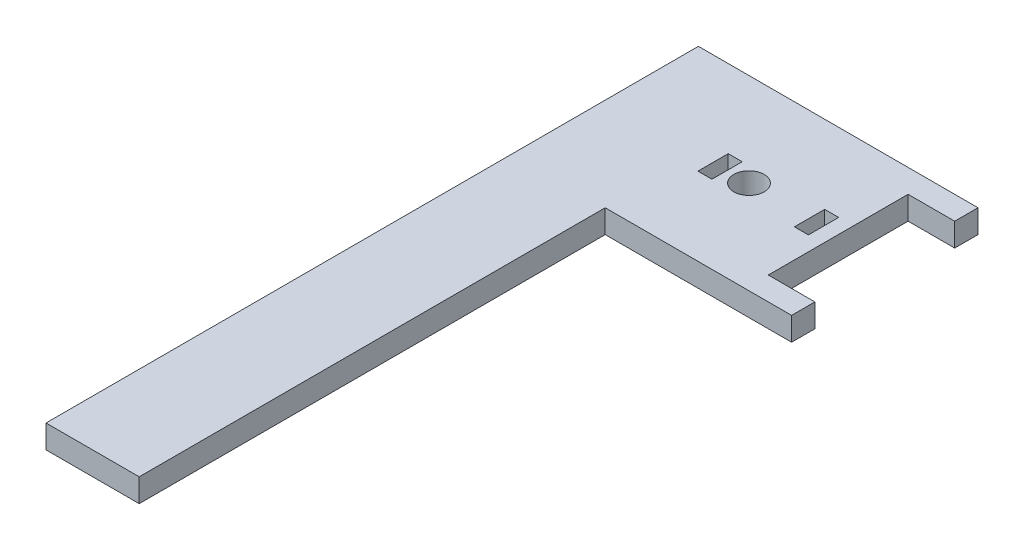
SolidWorks part; units mm, degrees
ref_plane "Front Plane" through (0, 0, 0) normal (0, 0, 1) x (1, 0, 0)
ref_plane "Top Plane" through (0, 0, 0) normal (0, 1, 0) x (1, 0, 0)
ref_plane "Right Plane" through (0, 0, 0) normal (1, 0, 0) x (0, 0, -1)
sketch "Sketch1" plane through (0, 0, 0) normal (0, 1, 0) x (1, 0, 0)
  line L1 (-30, -15) -> (30, -15)
  line L2 (-30, -15) -> (-30, 15)
  line L3 (-30, 15) -> (30, 15)
  line L4 (30, -15) -> (30, 15)
  line L5 (0, 15) -> (0, -15) construction
  line L6 (-30, 0) -> (30, 0) construction
  line L7 (-60, -20) -> (-20, -20)
  line L8 (-60, -20) -> (-60, 20)
  line L9 (-60, 20) -> (-20, 20)
  line L10 (-20, -20) -> (-20, 20)
  line L11 (-40, 20) -> (-40, -20) construction
  line L12 (-60, 0) -> (-20, 0) construction
  circle A0 centre (-49.15, 0) radius 3.25
  point P0 (0, 0)
  point P68 (-40, 0)
  dimension "D3" = 6.5
  dimension "D4" = 19.15
  dimension "D1" = 60
  dimension "D2" = 30
  dimension "D5" = 30
  dimension "D6" = 10
  dimension "D7" = 5
extrude "Boss-Extrude1" add sketch "Sketch1" along normal blind 5 contours L7 L10 L1 L2 L3 L9 L8 A0
sketch "Sketch3" plane through (0, 0, 0) normal (0, 1, 0) x (1, 0, 0)
  line L0 (-60, -20) -> (-20, -20) construction
  line L1 (-60, 20) -> (-80, 20)
  line L2 (-60, 20) -> (-60, -120)
  line L3 (-60, -120) -> (-80, -120)
  line L4 (-80, 20) -> (-80, -120)
  line L5 (-70, -120) -> (-70, 20) construction
  line L6 (-60, -50) -> (-80, -50) construction
  point P164 (-70, -50)
  dimension "D1" = 20
  dimension "D2" = 100
extrude "Boss-Extrude2" add sketch "Sketch3" along normal up to surface (5 mm away) up to face at (-49.15, 5, 3.25)
sketch "Sketch4" plane through (0, 5, 0) normal (0, 1, 0) x (1, 0, 0)
  line L0 (-30, 0) -> (-80, 0) construction
  line L1 (-30, -15) -> (-30, 15) construction
  line L2 (-80, 20) -> (-80, -120) construction
  line L4 (-36.15, 3.25) -> (-33.15, 3.25)
  line L5 (-36.15, 3.25) -> (-36.15, -3.25)
  line L6 (-36.15, -3.25) -> (-33.15, -3.25)
  line L7 (-33.15, 3.25) -> (-33.15, -3.25)
  line L8 (-34.65, -3.25) -> (-34.65, 3.25) construction
  line L9 (-36.15, 0) -> (-33.15, 0) construction
  line L10 (-56.85, 3.25) -> (-53.85, 3.25)
  line L11 (-56.85, 3.25) -> (-56.85, -3.25)
  line L12 (-56.85, -3.25) -> (-53.85, -3.25)
  line L13 (-53.85, 3.25) -> (-53.85, -3.25)
  line L14 (-55.35, -3.25) -> (-55.35, 3.25) construction
  line L15 (-56.85, 0) -> (-53.85, 0) construction
  point P7 (-34.65, 0)
  point P11 (-55.35, 0)
  dimension "D1" = 6.5
  dimension "D2" = 3
  dimension "D3" = 3.15
  dimension "D4" = 3
  dimension "D5" = 26.85
extrude "Cut-Extrude1" cut sketch "Sketch4" against normal through all both and the other way through all
